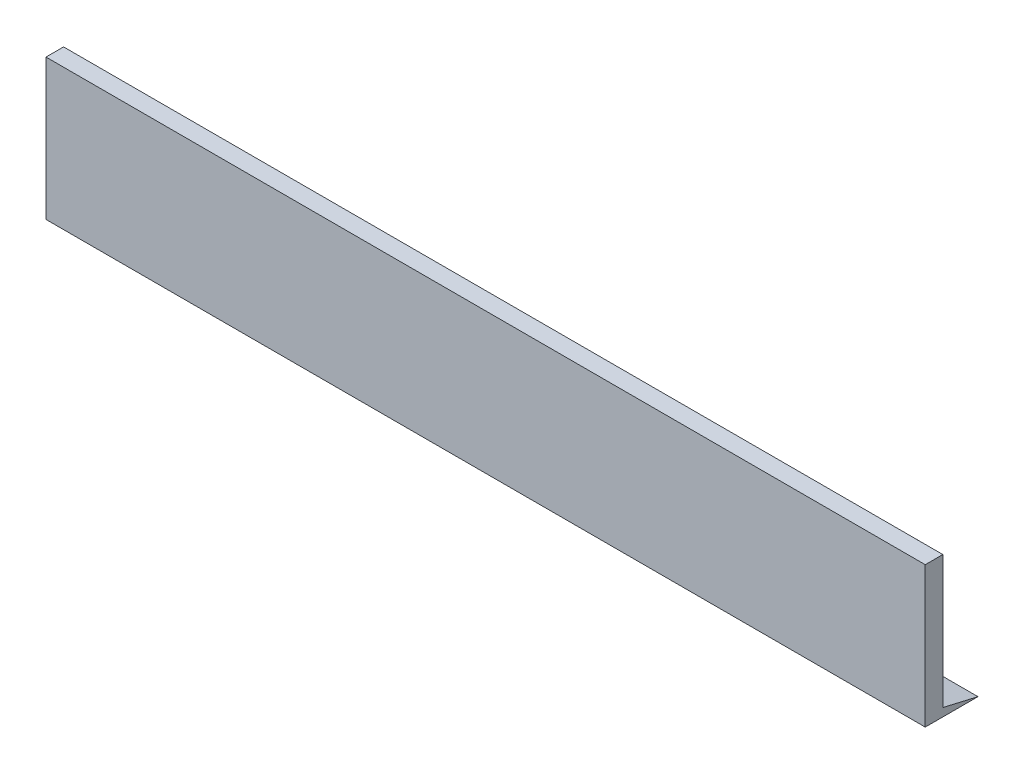
SolidWorks part; units mm, degrees
ref_plane "Plan de face" through (0, 0, 0) normal (0, 0, 1) x (1, 0, 0)
ref_plane "Plan de dessus" through (0, 0, 0) normal (0, 1, 0) x (1, 0, 0)
ref_plane "Plan de droite" through (0, 0, 0) normal (1, 0, 0) x (0, 0, -1)
sketch "Esquisse1" plane through (0, 0, 0) normal (0, 0, 1) x (1, 0, 0)
  line L1 (0, 0) -> (250, 0)
  line L2 (0, 0) -> (0, 40)
  line L3 (0, 40) -> (250, 40)
  line L4 (250, 0) -> (250, 40)
  dimension "D1" = 40
  dimension "D2" = 250
extrude "Boss.-Extru.1" add sketch "Esquisse1" along normal blind 5
sketch "Esquisse2" plane through (0, 0, 0) normal (-1, 0, 0) x (0, 0, 1)
  line L0 (0, 0) -> (-10, 0)
  line L1 (-10, 0) -> (0, 2.3206)
  line L2 (0, 40) -> (0, 0) construction
  line L3 (0, 2.3206) -> (0, 0)
  dimension "D1" = 10
extrude "Boss.-Extru.2" add sketch "Esquisse2" against normal up to surface (250 mm away) up to face at (250, 20, 2.5)
